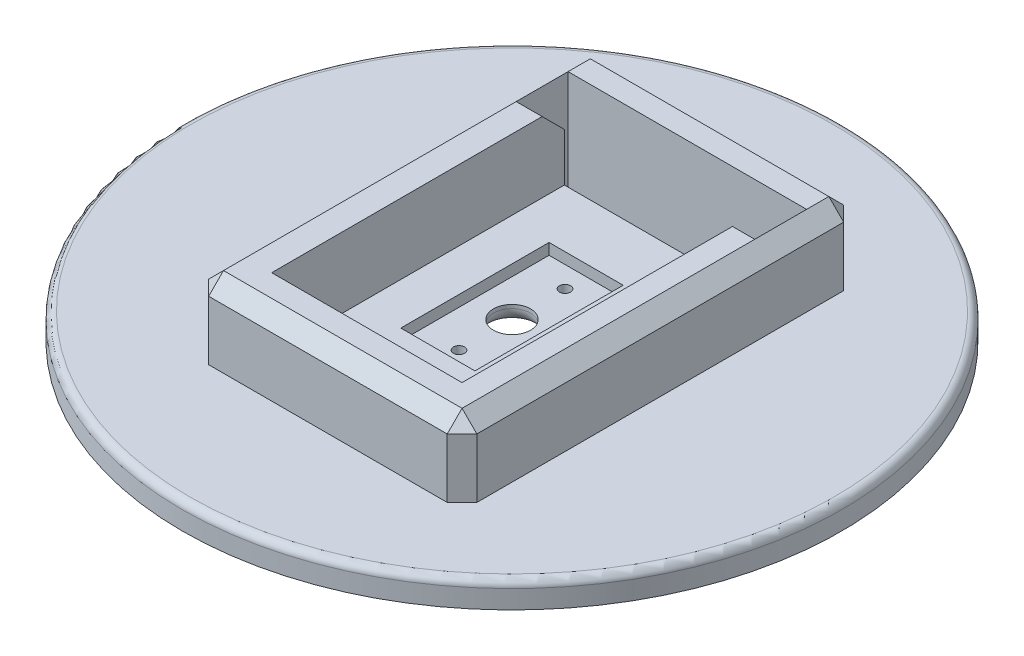
SolidWorks part; units mm, degrees
ref_plane "Front Plane" through (0, 0, 0) normal (0, 0, 1) x (1, 0, 0)
ref_plane "Top Plane" through (0, 0, 0) normal (0, 1, 0) x (1, 0, 0)
ref_plane "Right Plane" through (0, 0, 0) normal (1, 0, 0) x (0, 0, -1)
sketch "Sketch1" plane through (0, 0, 0) normal (0, 1, 0) x (1, 0, 0)
  circle A0 centre (0, 0) radius 44.45
extrude "Boss-Extrude1" add sketch "Sketch1" along normal blind 3.5
sketch "Sketch2" plane through (0, 3.5, 0) normal (0, 1, 0) x (1, 0, 0)
  line L0 (0, 0) -> (15, 0)
  line L1 (15, 0) -> (15, -21.7375)
  line L2 (15, 0) -> (15, 21.7375)
  line L3 (15, 21.7375) -> (-10.675, 21.7375)
  line L4 (-10.675, 21.7375) -> (-10.675, -21.7375)
  line L5 (-10.675, -21.7375) -> (15, -21.7375)
  dimension "D1" = 25.675
extrude "Cut-Extrude1" cut sketch "Sketch2" against normal blind 1 contours L2 L3 L4 L5 L1
sketch "Sketch3" plane through (0, 3.5, 0) normal (0, 1, 0) x (1, 0, 0)
  line L1 (15, -26.7375) -> (-16.175, -26.7375)
  line L5 (-16.175, -26.7375) -> (-16.175, 26.7375)
  line L6 (-16.175, 26.7375) -> (20, 26.7375)
  line L7 (20, 26.7375) -> (20, -26.7375)
  line L8 (20, -26.7375) -> (15, -26.7375)
  line L9 (15, -21.7375) -> (15, 21.7375)
  line L10 (-10.675, 21.7375) -> (-10.675, -21.7375)
  line L11 (-10.675, -21.7375) -> (15, -21.7375)
  line M6 (15, -21.7375) -> (-10.675, -21.7375)
  line M7 (-10.675, -21.7375) -> (-10.675, 21.7375)
  line M8 (-10.675, 21.7375) -> (15, 21.7375)
  line M9 (15, 21.7375) -> (15, -21.7375)
extrude "Boss-Extrude2" add sketch "Sketch3" along normal blind 10 contours L8 L7 L6 L5 L1 M9 M6 M7 M8
sketch "Sketch4" plane through (0, 2.5, 0) normal (0, 1, 0) x (1, 0, 0)
  line L0 (-10.675, 21.7375) -> (15, 21.7375)
  line L1 (15, 21.7375) -> (15, 17.7375)
  line L2 (15, 21.7375) -> (15, -21.7375) construction
  line L3 (15, 17.7375) -> (-10.675, 17.7375)
  line L4 (-10.675, -21.7375) -> (-10.675, 21.7375) construction
  line L5 (-10.675, 17.7375) -> (-10.675, 21.7375)
extrude "Cut-Extrude2" cut sketch "Sketch4" against normal blind 13
sketch "Sketch5" plane through (0, 2.5, 0) normal (0, 1, 0) x (1, 0, 0)
  line L0 (0, 0) -> (0, 6.4) construction
  line L1 (0, 0) -> (0, -6.4) construction
  line L2 (0, -6.4) -> (0, -7.15) construction
  line L3 (0, 6.4) -> (0, 7.15) construction
  circle A0 centre (0, 0) radius 10.25 construction
  circle A3 centre (0, -7.15) radius 0.75
  circle A4 centre (0, 7.15) radius 0.75
extrude "Cut-Extrude3" cut sketch "Sketch5" against normal blind 13
sketch "Sketch6" plane through (0, 0, 0) normal (0, -1, 0) x (1, 0, 0)
  circle A0 centre (0, 0) radius 2.5
  dimension "D1" = 5
extrude "Cut-Extrude4" cut sketch "Sketch6" against normal blind 13
fillet "Fillet1" radius 1 1 edges at (0, 3.5, 44.45)
chamfer "Chamfer1" distance 2 angle 45 8 edges at (-16.175, 8.5, -26.7375) (-16.175, 8.5, 26.7375) (20, 8.5, 26.7375) (20, 8.5, -26.7375) (1.9125, 13.5, -26.7375) (-16.175, 13.5, 0) (1.9125, 13.5, 26.7375) (20, 13.5, 0)
fillet "Fillet2" radius 2 1 edges at (0, 0, -2.5)
sketch "Sketch8" plane through (0, 13.5, 0) normal (0, 1, 0) x (1, 0, 0)
  line L5 (-10.675, 17.7375) -> (-14.175, 17.7375)
  line L6 (-14.175, 24.7375) -> (-14.175, -24.7375) construction
  line L7 (-14.175, 17.7375) -> (-14.175, 21.7375)
  line L8 (-14.175, 21.7375) -> (-10.675, 21.7375)
  line L9 (-10.675, 21.7375) -> (-10.675, 17.7375)
extrude "Cut-Extrude6" cut sketch "Sketch8" against normal through all
sketch "Sketch10" plane through (0, 13.5, 0) normal (0, 1, 0) x (1, 0, 0)
  line L0 (15, 17.7375) -> (18, 17.7375)
  line L1 (18, -24.7375) -> (18, 24.7375) construction
  line L2 (18, 17.7375) -> (18, 21.7375)
  line L3 (18, 21.7375) -> (15, 21.7375)
  line L4 (15, 21.7375) -> (15, 17.7375)
extrude "Cut-Extrude7" cut sketch "Sketch10" against normal through all
chamfer "Chamfer2" distance 3 angle 45 2 edges at (16.5, 13.5, -17.7375) (-12.425, 13.5, -17.7375)
sketch "Sketch11" plane through (0, 2.5, 0) normal (0, 1, 0) x (1, 0, 0)
  line L0 (15, -21.7375) -> (15, 17.7375)
  line L1 (15, 17.7375) -> (-10.675, 17.7375)
  line L2 (-10.675, 17.7375) -> (-10.675, -21.7375)
  line L3 (-10.675, -21.7375) -> (15, -21.7375)
  line L4 (0, 0) -> (5, 0)
  line L5 (5, 0) -> (5, -10)
  line L6 (5, -10) -> (-5, -10)
  line L7 (-5, -10) -> (-5, 10)
  line L8 (-5, 10) -> (5, 10)
  line L9 (5, 10) -> (5, 0)
  line M9 (15, 17.7375) -> (-10.675, 17.7375)
  line M10 (-10.675, 17.7375) -> (-10.675, -21.7375)
  line M11 (-10.675, -21.7375) -> (15, -21.7375)
  line M12 (15, -21.7375) -> (15, 17.7375)
extrude "Boss-Extrude3" add sketch "Sketch11" along normal blind 1.5 contours L8 L9 L5 L6 L7 M12 M9 M10 M11
